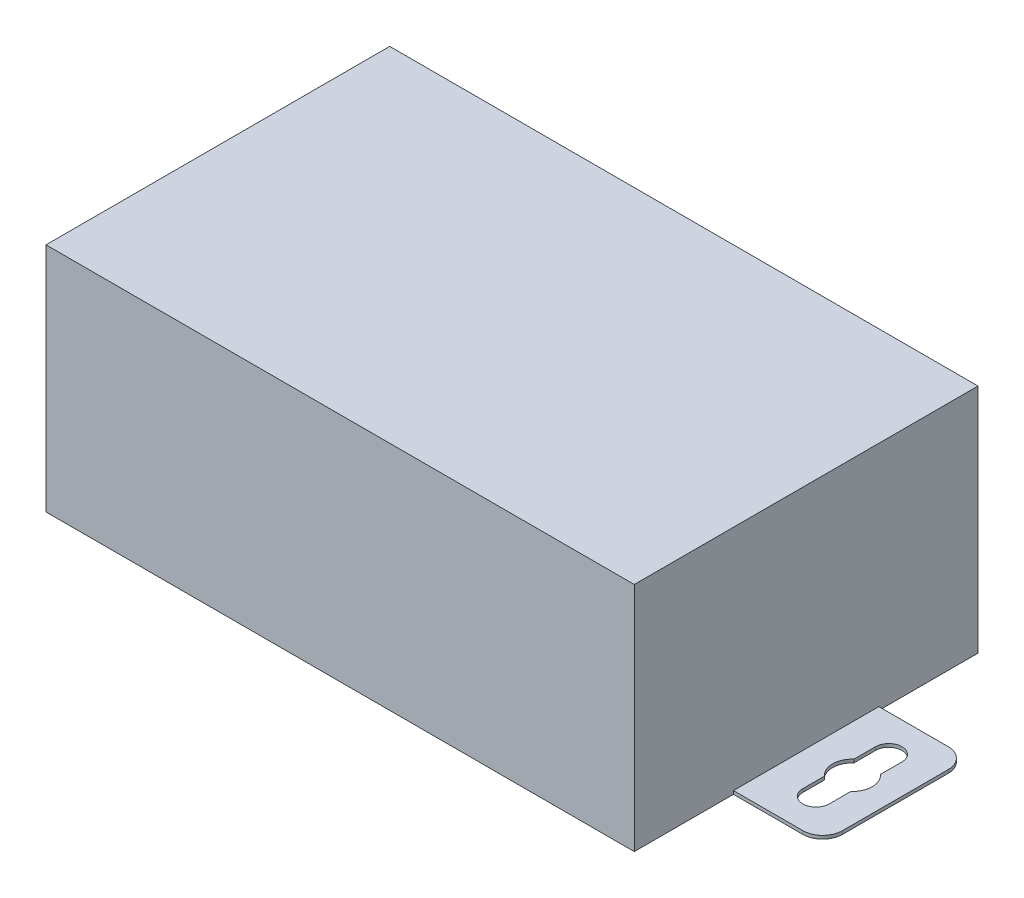
SolidWorks part; units mm, degrees
ref_plane "Спереди" through (0, 0, 0) normal (0, 0, 1) x (1, 0, 0)
ref_plane "Сверху" through (0, 0, 0) normal (0, 1, 0) x (1, 0, 0)
ref_plane "Справа" through (0, 0, 0) normal (1, 0, 0) x (0, 0, -1)
sketch "Эскиз1" plane through (0, 0, 0) normal (0, 1, 0) x (1, 0, 0)
  line L1 (0, 0) -> (89, 0)
  line L2 (0, 0) -> (0, 52)
  line L3 (0, 52) -> (89, 52)
  line L4 (89, 0) -> (89, 52)
  dimension "D1" = 52
  dimension "D2" = 89
extrude "Бобышка-Вытянуть1" add sketch "Эскиз1" along normal blind 35
sketch "Эскиз2" plane through (0, 0, 0) normal (0, -1, 0) x (1, 0, 0)
  line L0 (44.5, -1000) -> (44.5, 49000) construction
  line L1 (0, 0) -> (89, 0) construction
  line L2 (-1000, -26) -> (49000, -26) construction
  line L3 (0, -52) -> (0, 0) construction
  line L4 (-7, -20.5) -> (-7, -31.5) construction
  line L5 (-10.5, -37) -> (13.5, -37)
  line L6 (-13.5, -34) -> (-13.5, -18)
  line L7 (-10.5, -15) -> (13.5, -15)
  line L8 (13.5, -37) -> (13.5, -15)
  line L9 (-13.5, -37) -> (13.5, -15) construction
  line L10 (-13.5, -15) -> (13.5, -37) construction
  line L11 (-5, -20.5) -> (-5, -23.7639)
  line L12 (-9, -20.5) -> (-9, -23.7639)
  line L13 (-5, -28.2361) -> (-5, -31.5)
  line L14 (-9, -28.2361) -> (-9, -31.5)
  line L15 (102.5, -15) -> (75.5, -37) construction
  line L16 (102.5, -37) -> (75.5, -15) construction
  line L17 (96, -20.5) -> (96, -31.5) construction
  line L18 (98, -28.2361) -> (98, -31.5)
  line L19 (94, -28.2361) -> (94, -31.5)
  line L20 (98, -20.5) -> (98, -23.7639)
  line L21 (94, -20.5) -> (94, -23.7639)
  line L22 (75.5, -37) -> (75.5, -15)
  line L23 (99.5, -15) -> (75.5, -15)
  line L24 (102.5, -34) -> (102.5, -18)
  line L25 (99.5, -37) -> (75.5, -37)
  arc A0 (-5, -20.5) -> (-9, -20.5) centre (-7, -20.5) ccw
  arc A1 (-9, -31.5) -> (-5, -31.5) centre (-7, -31.5) ccw
  arc A2 (-9, -23.7639) -> (-9, -28.2361) centre (-7, -26) ccw
  arc A3 (-5, -28.2361) -> (-5, -23.7639) centre (-7, -26) ccw
  arc A4 (-10.5, -37) -> (-13.5, -34) centre (-10.5, -34) cw
  arc A5 (-13.5, -18) -> (-10.5, -15) centre (-10.5, -18) cw
  arc A6 (102.5, -18) -> (99.5, -15) centre (99.5, -18) ccw
  arc A7 (99.5, -37) -> (102.5, -34) centre (99.5, -34) ccw
  arc A8 (94, -28.2361) -> (94, -23.7639) centre (96, -26) cw
  arc A9 (98, -23.7639) -> (98, -28.2361) centre (96, -26) cw
  arc A10 (98, -31.5) -> (94, -31.5) centre (96, -31.5) cw
  arc A11 (94, -20.5) -> (98, -20.5) centre (96, -20.5) cw
  point P5 (44.5, 0)
  point P6 (0, -26)
  point P10 (0, -26)
  point P16 (-7, -26)
  point P54 (89, -26)
  dimension "D6" = 6
  dimension "D7" = 3
  dimension "D1" = 22
  dimension "D2" = 13.5
  dimension "D3" = 4.5
  dimension "D4" = 4
  dimension "D5" = 3.5
extrude "Бобышка-Вытянуть2" add sketch "Эскиз2" against normal blind 0.5
